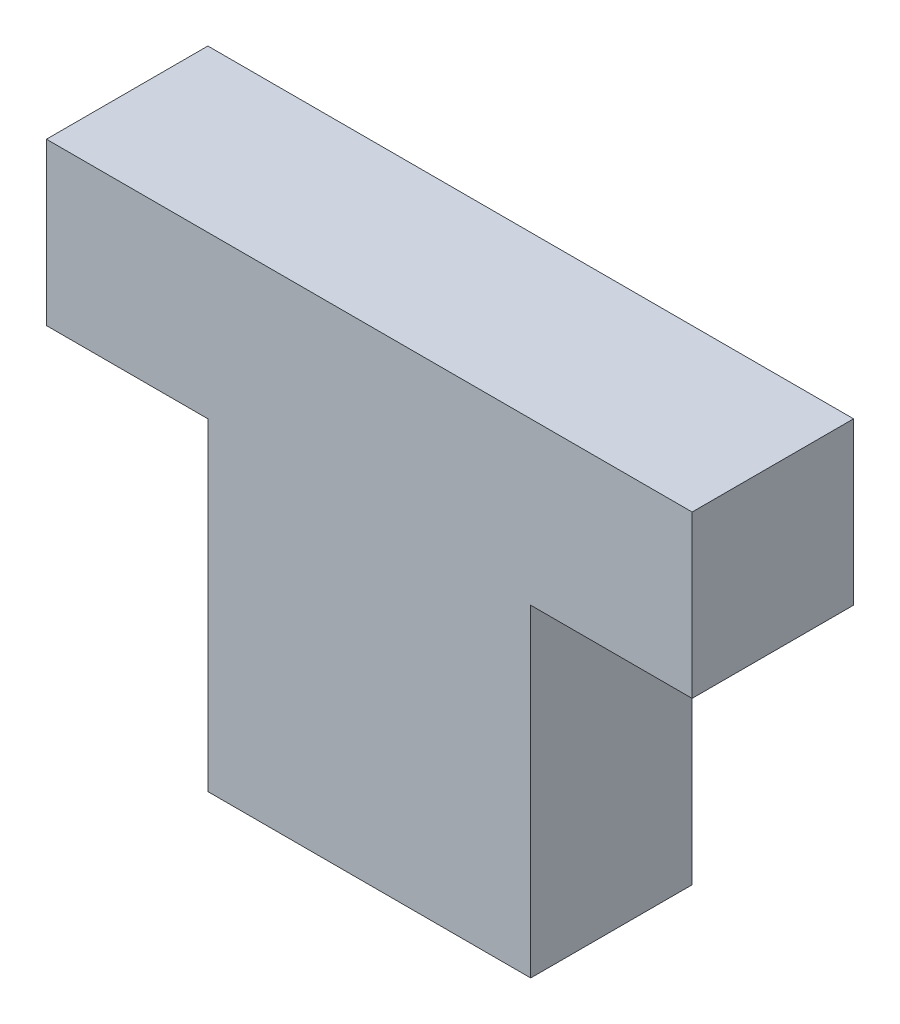
SolidWorks part; units mm, degrees
ref_plane "Front Plane" through (0, 0, 0) normal (0, 0, 1) x (1, 0, 0)
ref_plane "Top Plane" through (0, 0, 0) normal (0, 1, 0) x (1, 0, 0)
ref_plane "Right Plane" through (0, 0, 0) normal (1, 0, 0) x (0, 0, -1)
sketch "Sketch1" plane through (0, 0, 0) normal (0, 0, 1) x (1, 0, 0)
  line L0 (0, 0) -> (-10, 0)
  line L1 (0, 0) -> (0, 10)
  line L2 (-10, 0) -> (-10, 10)
  line L3 (0, 10) -> (-10, 10)
  line L4 (5, 10) -> (-15, 10)
  line L5 (5, 10) -> (5, 15)
  line L6 (-15, 10) -> (-15, 15)
  line L7 (5, 15) -> (-15, 15)
  point P0 (-5, 15)
  point P8 (-5, 0)
  dimension "D1" = 10
  dimension "D2" = 10
  dimension "D3" = 5
  dimension "D4" = 20
extrude "Boss-Extrude1" add sketch "Sketch1" along normal blind 5 contours L5 L7 L6 L4 L3 | L1 L3 L2 L0
